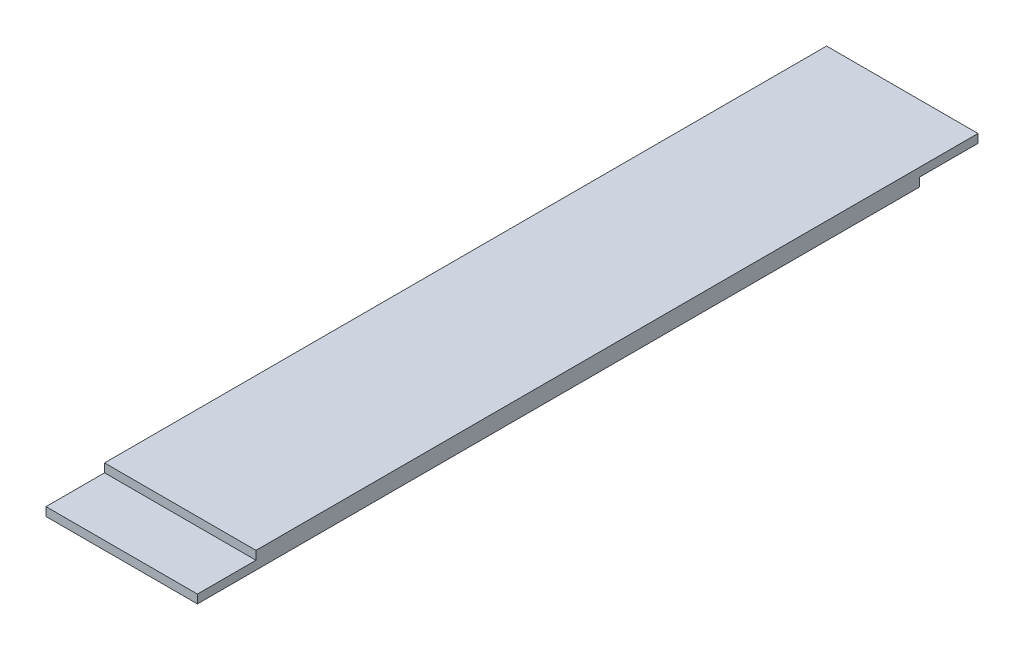
SolidWorks part; units mm, degrees
ref_plane "前基準面" through (0, 0, 0) normal (0, 0, 1) x (1, 0, 0)
ref_plane "上基準面" through (0, 0, 0) normal (0, 1, 0) x (1, 0, 0)
ref_plane "右基準面" through (0, 0, 0) normal (1, 0, 0) x (0, 0, -1)
sketch "草圖1" plane through (0, 0, 0) normal (0, 1, 0) x (1, 0, 0)
  line L1 (-19.4, -100) -> (19.4, -100)
  line L2 (-19.4, -100) -> (-19.4, 100)
  line L3 (-19.4, 100) -> (19.4, 100)
  line L4 (19.4, -100) -> (19.4, 100)
  line L5 (-19.4, -100) -> (19.4, 100) construction
  line L6 (-19.4, 100) -> (19.4, -100) construction
  point P0 (0, 0)
  dimension "D1" = 200
  dimension "D2" = 38.8
extrude "填料-伸長1" add sketch "草圖1" along normal blind 4.4
sketch "草圖2" plane through (0, 4.4, 0) normal (0, 1, 0) x (1, 0, 0)
  line L0 (19.4, -100) -> (19.4, 100) construction
  line L1 (-19.4, -100) -> (19.4, -100)
  line L2 (-19.4, -100) -> (-19.4, -85)
  line L3 (-19.4, -85) -> (19.4, -85)
  line L4 (19.4, -100) -> (19.4, -85)
  dimension "D1" = 15
extrude "除料-伸長1" cut sketch "草圖2" against normal blind 2.2
sketch "草圖3" plane through (0, 0, 0) normal (0, -1, 0) x (1, 0, 0)
  line L0 (19.4, 100) -> (19.4, -100) construction
  line L1 (-19.4, -100) -> (19.4, -100)
  line L2 (-19.4, -100) -> (-19.4, -85)
  line L3 (-19.4, -85) -> (19.4, -85)
  line L4 (19.4, -100) -> (19.4, -85)
  dimension "D1" = 15
extrude "除料-伸長2" cut sketch "草圖3" against normal blind 2.2
